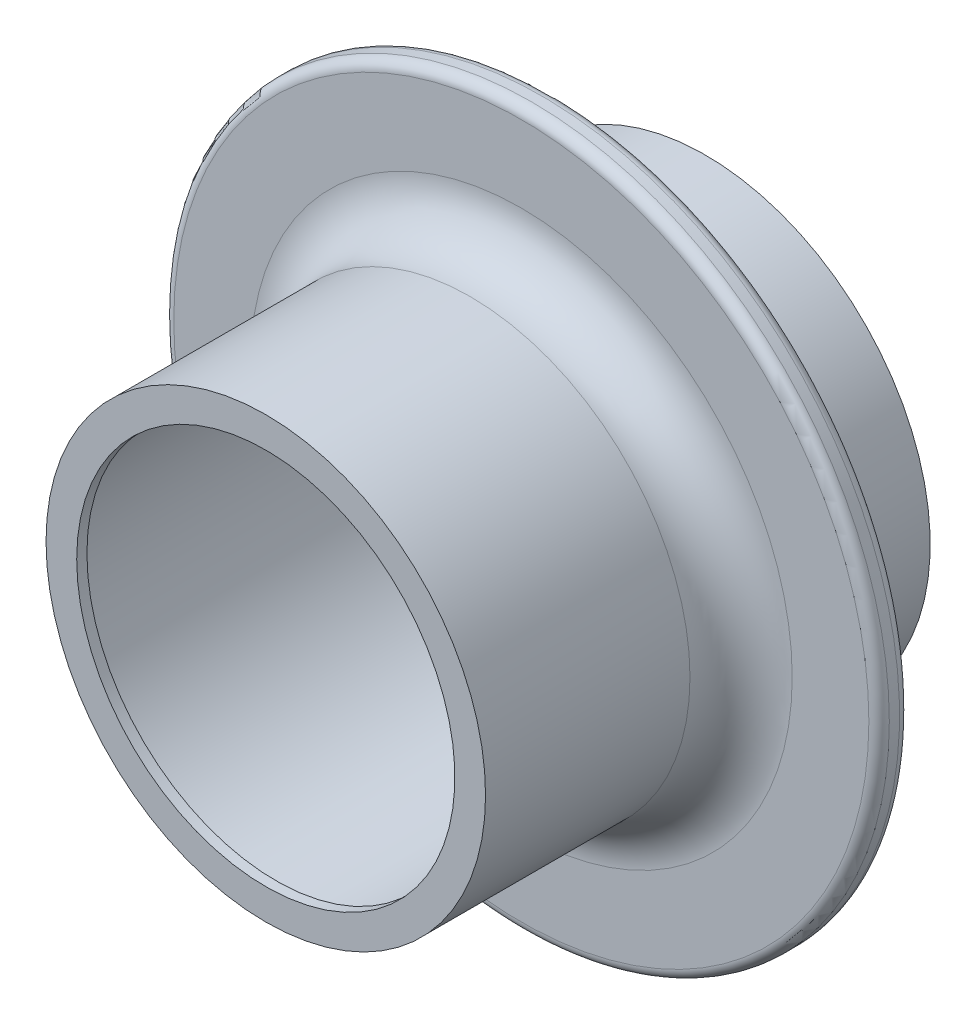
SolidWorks part; units mm, degrees
material "2024 合金"
ref_plane "正面" through (0, 0, 0) normal (0, 0, 1) x (1, 0, 0)
ref_plane "平面" through (0, 0, 0) normal (0, 1, 0) x (1, 0, 0)
ref_plane "右側面" through (0, 0, 0) normal (1, 0, 0) x (0, 0, -1)
sketch "ｽｹｯﾁ1" plane through (0, 0, 0) normal (0, 0, 1) x (1, 0, 0)
  circle A0 centre (0, 0) radius 35
  dimension "D1" = 70
extrude "ﾎﾞｽ - 押し出し1" add sketch "ｽｹｯﾁ1" along normal blind 43
sketch "ｽｹｯﾁ2" plane through (0, 0, 0) normal (0, 0, -1) x (-1, 0, 0)
  circle A0 centre (0, 0) radius 22
  circle A1 centre (0, 0) radius 35
  circle A2 centre (0, 0) radius 35 construction
  dimension "D1" = 44
extrude "ｶｯﾄ - 押し出し1" cut sketch "ｽｹｯﾁ2" against normal blind 15
sketch "ｽｹｯﾁ3" plane through (0, 0, 43) normal (0, 0, 1) x (1, 0, 0)
  circle A0 centre (0, 0) radius 21.5
  circle A1 centre (0, 0) radius 35
  circle A2 centre (0, 0) radius 35 construction
  dimension "D1" = 43
extrude "ｶｯﾄ - 押し出し2" cut sketch "ｽｹｯﾁ3" against normal blind 25
sketch "ｽｹｯﾁ4" plane through (0, 0, 0) normal (0, 0, -1) x (-1, 0, 0)
  circle A0 centre (0, 0) radius 18.5
  dimension "D1" = 37
extrude "ｶｯﾄ - 押し出し3" cut sketch "ｽｹｯﾁ4" against normal through all
sketch "ｽｹｯﾁ5" plane through (0, 0, 0) normal (0, 0, -1) x (-1, 0, 0)
  circle A0 centre (0, 0) radius 20
  dimension "D1" = 40
extrude "ｶｯﾄ - 押し出し4" cut sketch "ｽｹｯﾁ5" against normal blind 42
fillet "ﾌｨﾚｯﾄ1" radius 5 2 edges at (21.5, 0, 18) (-22, 0, 15)
fillet "ﾌｨﾚｯﾄ2" radius 1 2 edges at (35, 0, 18) (-35, 0, 15)
